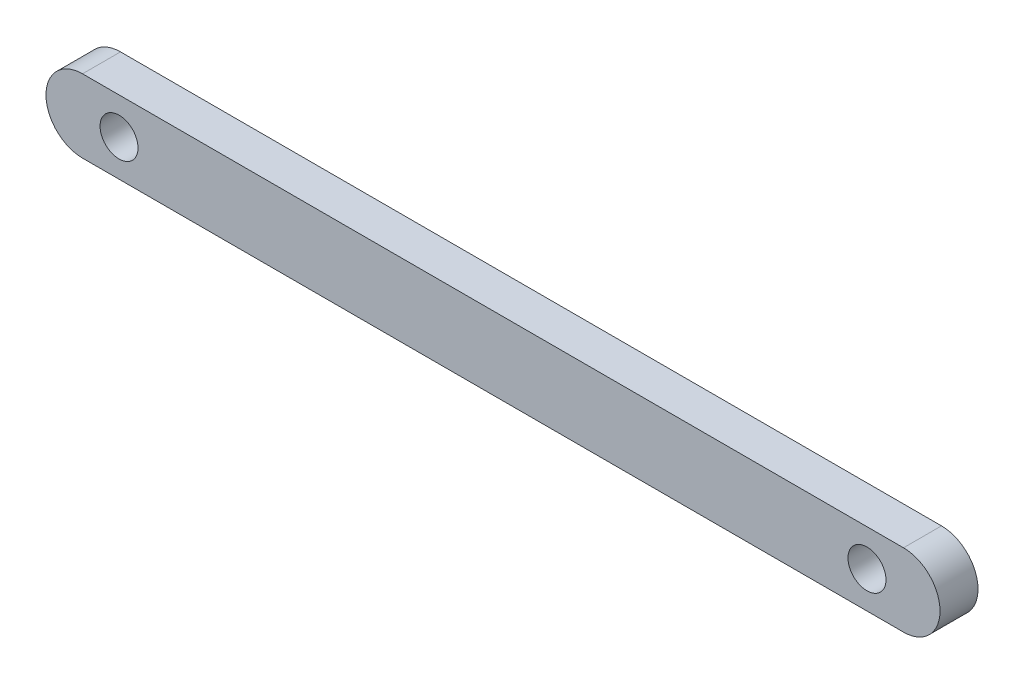
SolidWorks part; units mm, degrees
ref_plane "Front" through (0, 0, 0) normal (0, 0, 1) x (1, 0, 0)
ref_plane "Top" through (0, 0, 0) normal (0, 1, 0) x (1, 0, 0)
ref_plane "Right" through (0, 0, 0) normal (1, 0, 0) x (0, 0, -1)
sketch "Sketch1" plane through (0, 0, 0) normal (0, 0, 1) x (1, 0, 0)
  line L0 (0, 0) -> (71.374, 0) construction
  line L1 (0, 3.175) -> (71.374, 3.175)
  line L2 (0, -3.175) -> (71.374, -3.175)
  line L3 (-3.175, 0) -> (0, 0) construction
  line L4 (71.374, 0) -> (74.549, 0) construction
  line L5 (35.687, 0) -> (35.687, 3.175) construction
  arc A0 (0, 3.175) -> (0, -3.175) centre (0, 0) ccw
  arc A1 (71.374, -3.175) -> (71.374, 3.175) centre (71.374, 0) ccw
  circle A2 centre (3.175, 0) radius 1.651
  circle A3 centre (68.199, 0) radius 1.651
  point P3 (35.687, 0)
  dimension "D3" = 3.302
  dimension "D1" = 77.724
  dimension "D2" = 6.35
  dimension "D4" = 65.024
extrude "Boss-Extrude1" add sketch "Sketch1" along normal blind 3.302
